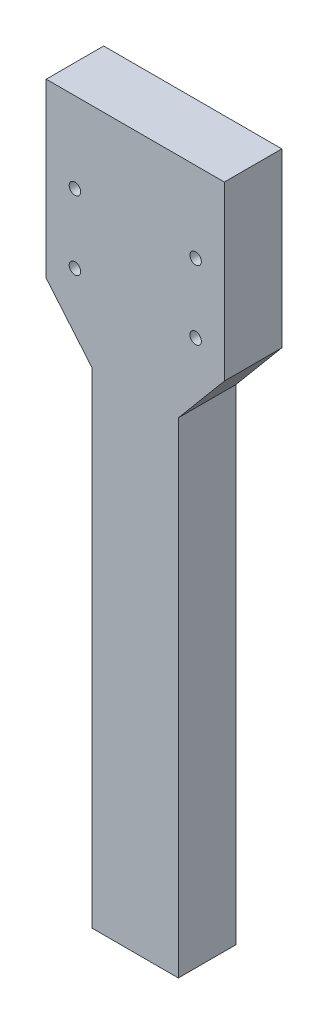
SolidWorks part; units mm, degrees
ref_plane "Front Plane" through (0, 0, 0) normal (0, 0, 1) x (1, 0, 0)
ref_plane "Top Plane" through (0, 0, 0) normal (0, 1, 0) x (1, 0, 0)
ref_plane "Right Plane" through (0, 0, 0) normal (1, 0, 0) x (0, 0, -1)
sketch "Sketch1" plane through (0, 0, 0) normal (0, 0, 1) x (1, 0, 0)
  line L14 (15, 84.426) -> (23, 93.96)
  line L15 (0, 0) -> (15, 0)
  line L17 (0, 123.96) -> (15, 123.96)
  line L19 (23, 93.96) -> (23, 123.96)
  line L20 (23, 123.96) -> (15, 123.96)
  line L21 (7.5, 123.96) -> (7.5, 0) construction
  line L22 (15, 123.96) -> (15, 84.426) construction
  line L23 (15, 0) -> (15, 84.426)
  line L24 (0, 0) -> (0, 84.426)
  line L25 (0, 84.426) -> (-8, 93.96)
  line L26 (-8, 123.96) -> (0, 123.96)
  line L27 (-8, 93.96) -> (-8, 123.96)
  line L28 (-3, 97.96) -> (-3, 109.96) construction
  circle A0 centre (-3, 109.96) radius 1
  circle A1 centre (-3, 97.96) radius 1
  circle A2 centre (18, 97.96) radius 1
  circle A3 centre (18, 109.96) radius 1
  dimension "D8" = 2
  dimension "D1" = 15
  dimension "D2" = 123.96
  dimension "D3" = 30
  dimension "D4" = 140
  dimension "D5" = 8
  dimension "D6" = 12
  dimension "D7" = 14
  dimension "D9" = 10.5
extrude "Boss-Extrude1" add sketch "Sketch1" along normal blind 10
